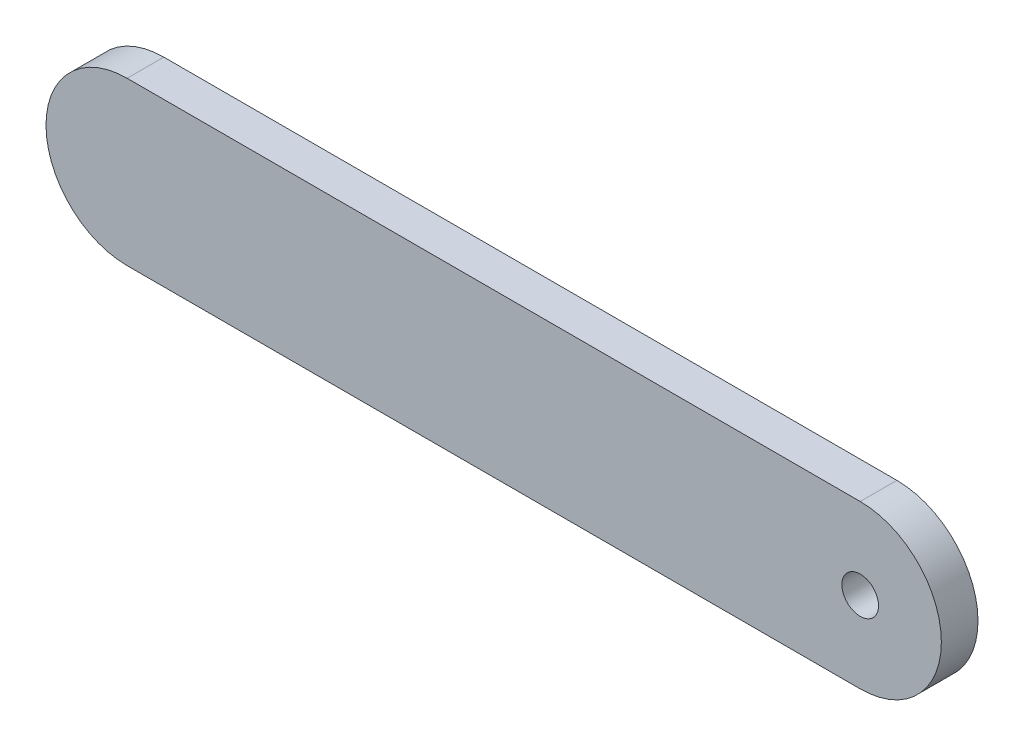
SolidWorks part; units mm, degrees
ref_plane "Front Plane" through (0, 0, 0) normal (0, 0, 1) x (1, 0, 0)
ref_plane "Top Plane" through (0, 0, 0) normal (0, 1, 0) x (1, 0, 0)
ref_plane "Right Plane" through (0, 0, 0) normal (1, 0, 0) x (0, 0, -1)
sketch "Sketch1" plane through (0, 0, 0) normal (0, 0, 1) x (1, 0, 0)
  line L0 (-18.3965, 0) -> (41.6035, 0) construction
  line L1 (-18.3965, 6.6421) -> (41.6035, 6.6421)
  line L2 (-18.3965, -6.6421) -> (41.6035, -6.6421)
  arc A0 (-18.3965, 6.6421) -> (-18.3965, -6.6421) centre (-18.3965, 0) ccw
  arc A1 (41.6035, -6.6421) -> (41.6035, 6.6421) centre (41.6035, 0) ccw
  circle A2 centre (41.6035, 0) radius 1.5
  point P3 (11.6035, 0)
  dimension "D1" = 3
  dimension "D2" = 60
extrude "Boss-Extrude1" add sketch "Sketch1" along normal blind 3
